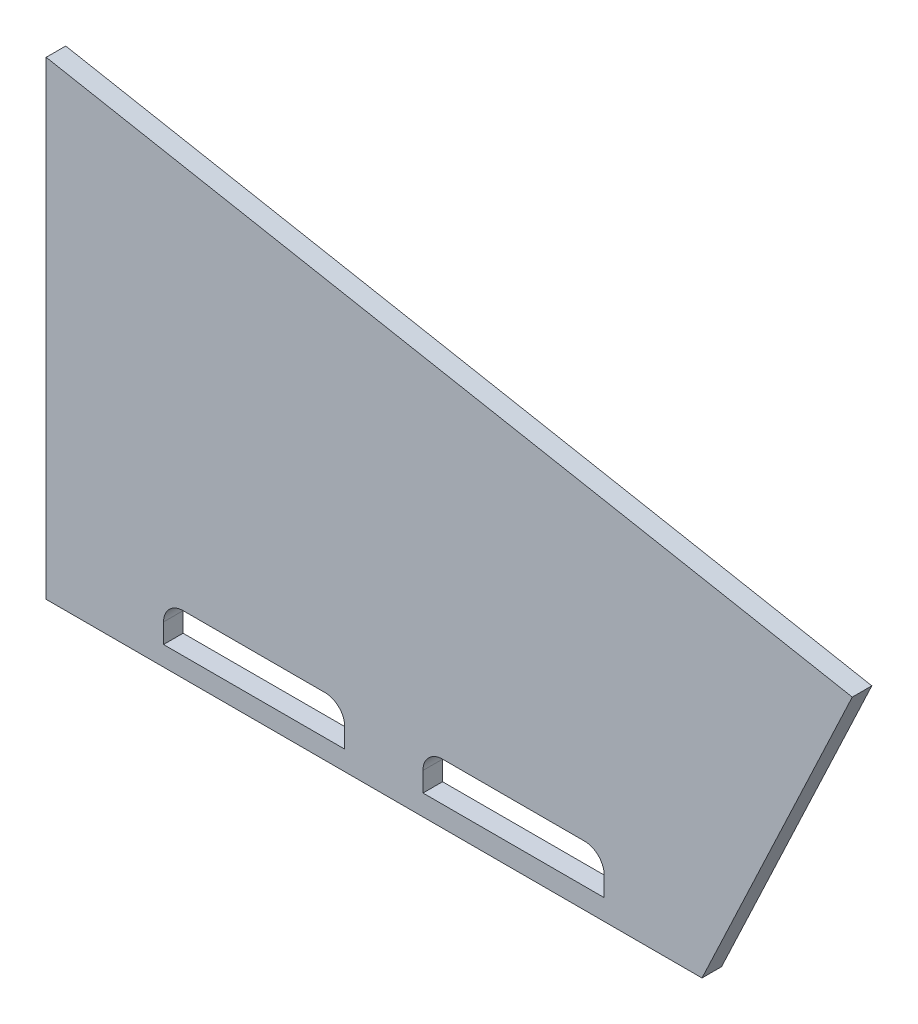
SolidWorks part; units mm, degrees
ref_plane "Front Plane" through (0, 0, 0) normal (0, 0, 1) x (1, 0, 0)
ref_plane "Top Plane" through (0, 0, 0) normal (0, 1, 0) x (1, 0, 0)
ref_plane "Right Plane" through (0, 0, 0) normal (1, 0, 0) x (0, 0, -1)
sketch "Sketch1" plane through (0, 0, 0) normal (0, 0, 1) x (1, 0, 0)
  line L0 (12.7, 22.225) -> (12.7, 327.025) construction
  line L1 (12.7, 22.225) -> (12.7, 327.025)
  line L2 (438.5213, 22.225) -> (536.0898, 228.9575) construction
  line L3 (438.5213, 22.225) -> (536.0898, 228.9575)
  line L4 (12.7, 22.225) -> (438.5213, 22.225)
  line L5 (12.7, 327.025) -> (536.0898, 228.9575)
extrude "Boss-Extrude1" add sketch "Sketch1" against normal blind 12.7
sketch "Sketch2" plane through (0, 0, 0) normal (0, 0, 1) x (1, 0, 0)
  line L0 (12.7, 22.225) -> (438.5213, 22.225) construction
  line L1 (88.9, 34.925) -> (206.5606, 34.925)
  line L2 (88.9, 34.925) -> (88.9, 60.325)
  line L3 (88.9, 60.325) -> (206.5606, 60.325)
  line L4 (206.5606, 34.925) -> (206.5606, 60.325)
  line L5 (257.3606, 35.6557) -> (375.0213, 35.6557)
  line L6 (257.3606, 35.6557) -> (257.3606, 61.0557)
  line L7 (257.3606, 61.0557) -> (375.0213, 61.0557)
  line L8 (375.0213, 35.6557) -> (375.0213, 61.0557)
  line L9 (12.7, 327.025) -> (12.7, 22.225) construction
  dimension "D1" = 12.7
  dimension "D2" = 76.2
  dimension "D3" = 50.8
  dimension "D4" = 63.5
  dimension "D5" = 25.4
extrude "Cut-Extrude1" cut sketch "Sketch2" against normal through all
fillet "Fillet1" radius 12.7 4 edges at (375.0213, 61.0557, -6.35) (257.3606, 61.0557, -6.35) (206.5606, 60.325, -6.35) (88.9, 60.325, -6.35)
